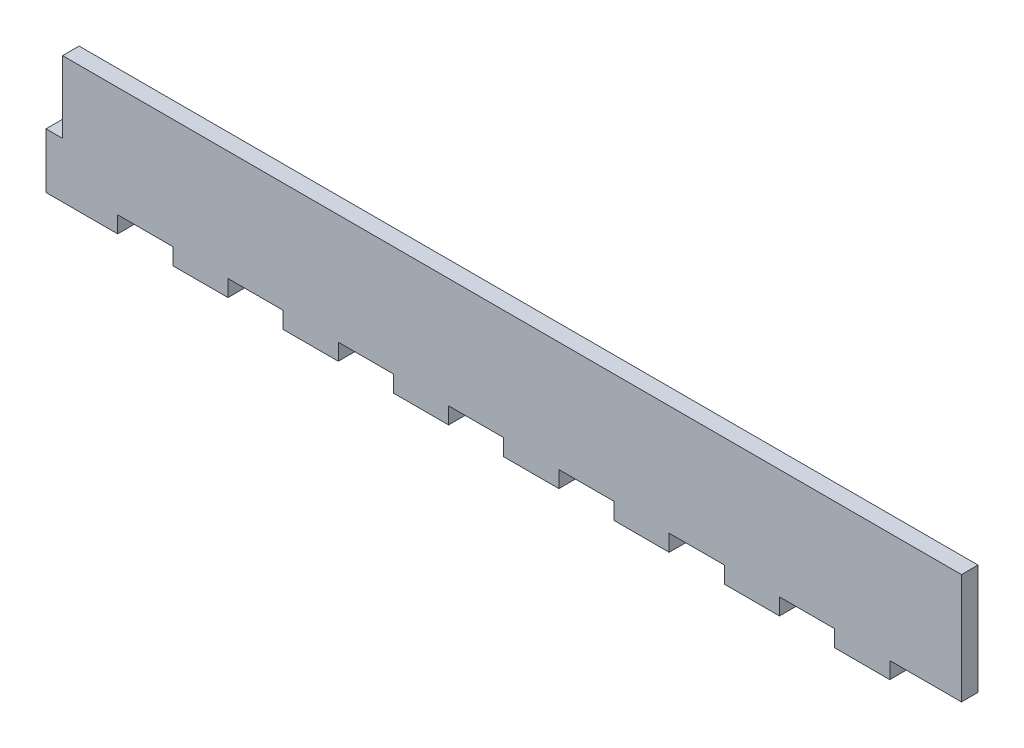
SolidWorks part; units mm, degrees
ref_plane "Plan de face" through (0, 0, 0) normal (0, 0, 1) x (1, 0, 0)
ref_plane "Plan de dessus" through (0, 0, 0) normal (0, 1, 0) x (1, 0, 0)
ref_plane "Plan de droite" through (0, 0, 0) normal (1, 0, 0) x (0, 0, -1)
sketch "Esquisse1" plane through (0, 0, 0) normal (0, 0, 1) x (1, 0, 0)
  line L1 (0, 0) -> (163, 0)
  line L2 (0, 0) -> (0, -20)
  line L3 (0, -20) -> (163, -20)
  line L4 (163, 0) -> (163, -20)
  dimension "D1" = 163
  dimension "D2" = 20
extrude "Boss.-Extru.1" add sketch "Esquisse1" along normal blind 3
sketch "Esquisse2" plane through (0, -20, 0) normal (0, -1, 0) x (1, 0, 0)
  line L0 (0, 0) -> (163, 0) construction
  line L1 (0, 3) -> (10, 3)
  line L2 (0, 3) -> (0, 0)
  line L3 (0, 0) -> (10, 0)
  line L4 (10, 3) -> (10, 0)
  dimension "D1" = 10
extrude "Boss.-Extru.2" add sketch "Esquisse2" along normal blind 3
pattern_linear "Répétition linéaire1" count 8 spacing 20 along (1, 0, 0) of "Boss.-Extru.2"
sketch "Esquisse3" plane through (0, 0, 0) normal (-1, 0, 0) x (0, 0, 1)
  line L0 (3, 0) -> (3, -23) construction
  line L1 (0, -23) -> (3, -23)
  line L2 (0, -23) -> (0, -13)
  line L3 (0, -13) -> (3, -13)
  line L4 (3, -23) -> (3, -13)
  dimension "D1" = 10
extrude "Boss.-Extru.3" add sketch "Esquisse3" along normal blind 3
